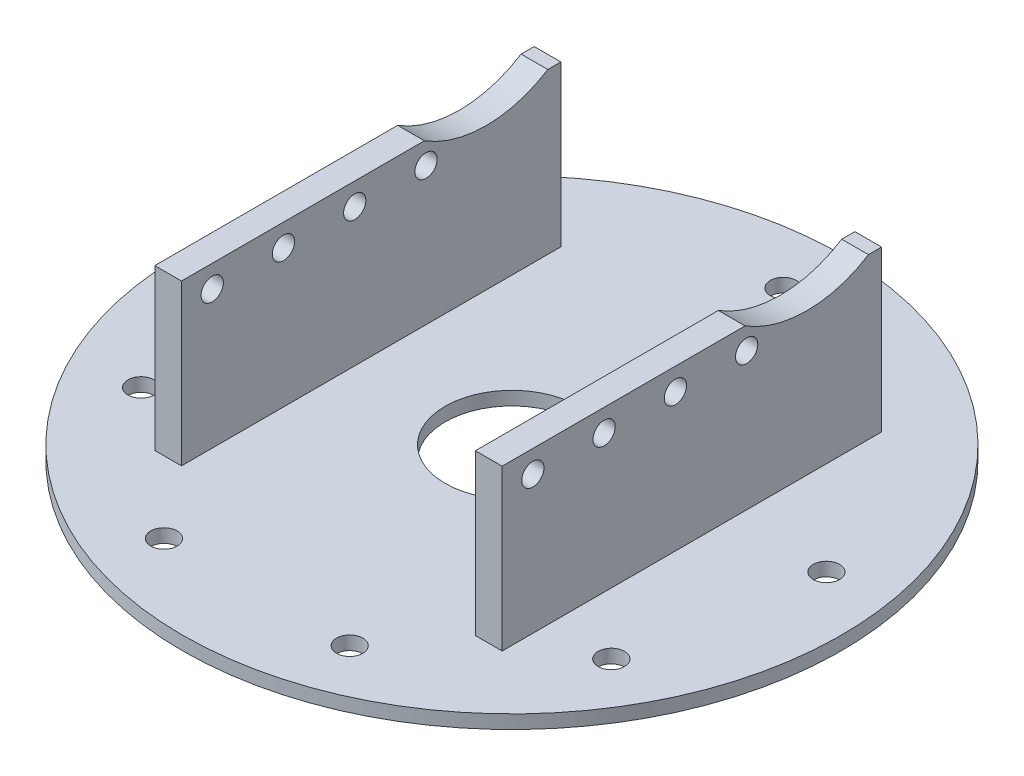
SolidWorks part; units mm, degrees
ref_plane "Ön Düzlem" through (0, 0, 0) normal (0, 0, 1) x (1, 0, 0)
ref_plane "Üst Düzlem" through (0, 0, 0) normal (0, 1, 0) x (1, 0, 0)
ref_plane "Sağ Düzlem" through (0, 0, 0) normal (1, 0, 0) x (0, 0, -1)
ref_plane "Düzlem1" through (0, 0, 0) normal (0, 0, -1) x (-1, 0, 0)
sketch "Çizim1" plane through (0, 0, 0) normal (0, 0, -1) x (-1, 0, 0)
  line L0 (-37, 0) -> (0, 0)
  line L1 (0, 0) -> (0, 1.524)
  line L2 (0, 1.524) -> (-37, 1.524)
  line L3 (-37, 1.524) -> (-37, 0)
  line L4 (0, 0) -> (0, 1.524) construction
revolve "Döndür1" add sketch "Çizim1" angle 360 about L4
sketch "Çizim2" plane through (0, 1.524, 0) normal (0, 1, 0) x (-1, 0, 0)
  line L0 (15, 20.6) -> (18, 20.6)
  line L1 (18, 20.6) -> (18, -22)
  line L2 (18, -22) -> (15, -22)
  line L3 (15, -22) -> (15, 20.6)
extrude "Yükseklik-Ekstrüzyon1" add sketch "Çizim2" along normal blind 16.276
sketch "Çizim3" plane through (0, 1.524, 0) normal (0, 1, 0) x (-1, 0, 0)
  line L0 (-18, 20.6) -> (-15, 20.6)
  line L1 (-15, 20.6) -> (-15, -22)
  line L2 (-15, -22) -> (-18, -22)
  line L3 (-18, -22) -> (-18, 20.6)
extrude "Yükseklik-Ekstrüzyon2" add sketch "Çizim3" along normal blind 16.276
hole_wizard "Delik1" positions "Çizim5" profile "Çizim4" legacy
sketch "Çizim5" plane through (0, 1.524, 0) normal (0, 1, 0) x (1, 0, 0)
  point P0 (0, 30.48)
  point P1 (30.0169, 5.2928)
  point P2 (26.3965, -15.24)
  point P3 (10.4248, -28.6418)
  point P4 (-10.4248, -28.6418)
  point P5 (-26.3965, -15.24)
  point P6 (-30.0169, 5.2928)
sketch "Çizim4" plane through (0, 1.524, -30.48) normal (1, 0, 0) x (0, 0, 1)
  line L0 (0, 0) -> (0, 1.524)
  line L1 (0, 1.524) -> (1.4783, 1.524)
  line L2 (1.4783, 1.524) -> (1.4783, 0)
  line L3 (1.4783, 0) -> (0, 0)
  line L4 (0, 110) -> (0, -10) construction
  dimension "Diameter" = 2.9566
  dimension "Depth" = 1.524
hole_wizard "Ø0.15 (0.15) Diameter Hole1" positions "Çizim7" profile "Çizim6" hole size "Ø0.15" standard "Ansi Metric"
sketch "Çizim7" plane through (0, 0, 0) normal (0, -1, 0) x (-1, 0, 0)
  point P0 (0, 0)
sketch "Çizim6" plane through (0, 0, 0) normal (1, 0, 0) x (0, 0, -1)
  line L0 (0, 0) -> (0, 17.8)
  line L1 (0, 17.8) -> (7.5, 17.8)
  line L2 (7.5, 17.8) -> (7.5, 0)
  line L5 (7.5, 0) -> (0, 0)
  line L11 (0, -6.35) -> (0, 107.95) construction
  dimension "Thru Hole Dia." = 15
  dimension "Thru Hole Depth" = 17.8
sketch "Çizim15" plane through (0, 17.8, 0) normal (0, 1, 0) x (1, 0, 0)
  line L0 (-15, -20.6) -> (-15, 22) construction
  line L1 (-16.5, 24.4754) -> (16.5, 24.4754)
  line L2 (-16.5, 24.4754) -> (-16.5, -24.2182)
  line L3 (-16.5, -24.2182) -> (16.5, -24.2182)
  line L4 (16.5, 24.4754) -> (16.5, -24.2182)
  line L5 (15, 22) -> (15, -20.6) construction
  dimension "D1" = 33
  dimension "D2" = 1.5
  dimension "D3" = 1.5
extrude "Kes-Ekstrüzyon2" cut sketch "Çizim15" against normal up to surface (16.276 mm away) up to face at (0, 1.524, 7.5)
sketch "Çizim16" plane through (18, 0, 0) normal (1, 0, 0) x (0, 0, -1)
  line L1 (-20.6, 17.8) -> (22, 17.8)
  line L2 (-20.6, 17.8) -> (-20.6, 1.524)
  line L3 (-20.6, 1.524) -> (22, 1.524)
  line L4 (22, 17.8) -> (22, 1.524)
extrude "Yükseklik-Ekstrüzyon3" add sketch "Çizim16" along normal blind 1.5
sketch "Çizim17" plane through (-18, 0, 0) normal (-1, 0, 0) x (0, 0, 1)
  line L1 (-22, 17.8) -> (20.6, 17.8)
  line L2 (-22, 17.8) -> (-22, 1.524)
  line L3 (-22, 1.524) -> (20.6, 1.524)
  line L4 (20.6, 17.8) -> (20.6, 1.524)
extrude "Yükseklik-Ekstrüzyon4" add sketch "Çizim17" along normal blind 1.5
sketch "Çizim18" plane through (-19.5, 0, 0) normal (-1, 0, 0) x (0, 0, 1)
  line L1 (-22, 17.8) -> (20.6, 17.8)
  line L2 (-22, 17.8) -> (-22, 19.5)
  line L3 (-22, 19.5) -> (20.6, 19.5)
  line L4 (20.6, 17.8) -> (20.6, 19.5)
  dimension "D1" = 1.7
extrude "Yükseklik-Ekstrüzyon5" add sketch "Çizim18" against normal up to surface (3 mm away) up to face at (-16.5, 9.662, -0.7)
sketch "Çizim19" plane through (19.5, 0, 0) normal (1, 0, 0) x (0, 0, -1)
  line L1 (-20.6, 19.5) -> (22, 19.5)
  line L2 (-20.6, 19.5) -> (-20.6, 17.8)
  line L3 (-20.6, 17.8) -> (22, 17.8)
  line L4 (22, 19.5) -> (22, 17.8)
extrude "Yükseklik-Ekstrüzyon6" add sketch "Çizim19" against normal up to surface (3 mm away) up to face at (16.5, 9.662, -0.7)
sketch "Çizim20" plane through (-19.5, 0, 0) normal (-1, 0, 0) x (0, 0, 1)
  circle A0 centre (-13.6, 30.5) radius 13
  dimension "D3" = 26
extrude "Kes-Ekstrüzyon3" cut sketch "Çizim20" against normal up to surface (39 mm away) up to face at (19.5, 10.512, -0.7)
sketch "Çizim21" plane through (-19.5, 0, 0) normal (-1, 0, 0) x (0, 0, 1)
  line L0 (20.6, 19.5) -> (-6.6718, 19.5) construction
  line L1 (20.6, 1.524) -> (20.6, 19.5) construction
  circle A0 centre (17.15, 17) radius 1.25
  circle A1 centre (9.15, 17) radius 1.25
  circle A2 centre (1.15, 17) radius 1.25
  circle A3 centre (-6.85, 17) radius 1.25
  dimension "D1" = 2.5
  dimension "D2" = 3.45
  dimension "D3" = 2.5
  dimension "D4" = 2.5
  dimension "D5" = 2.5
  dimension "D6" = 2.5
  dimension "D7" = 8
  dimension "D8" = 8
  dimension "D9" = 8
extrude "Kes-Ekstrüzyon4" cut sketch "Çizim21" against normal up to surface (39 mm away) up to face at (19.5, 13.1747, -5)
